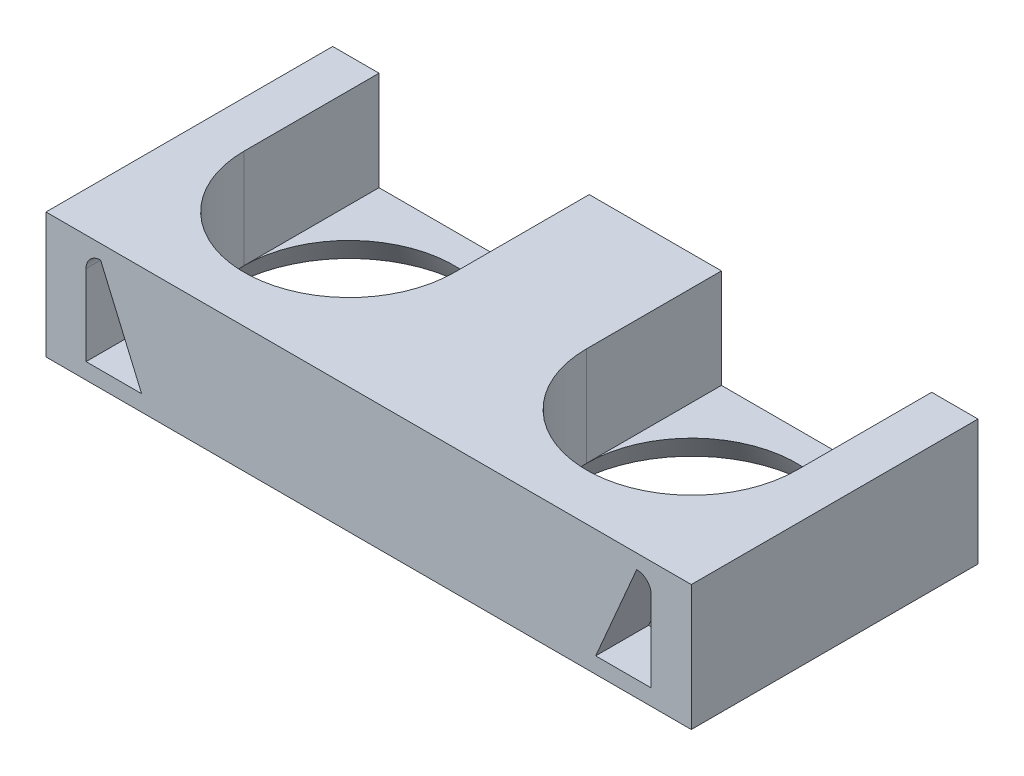
SolidWorks part; units mm, degrees
ref_plane "Alzado" through (0, 0, 0) normal (0, 0, 1) x (1, 0, 0)
ref_plane "Planta" through (0, 0, 0) normal (0, 1, 0) x (1, 0, 0)
ref_plane "Vista lateral" through (0, 0, 0) normal (1, 0, 0) x (0, 0, -1)
ref_plane "Plano1" through (0, -4.9, 0) normal (0, -1, 0) x (-1, 0, 0)
sketch "Croquis2" plane through (0, -4.9, 0) normal (0, -1, 0) x (-1, 0, 0)
  line L0 (-5, 20.4) -> (5, 20.4)
  line L1 (-12.95, 10.2) -> (12.95, 10.2) construction
  line L2 (-20.9, 10.2) -> (-20.9, 20.4)
  line L3 (20.9, 10.2) -> (20.9, 20.4)
  line L4 (-5, 10.2) -> (-5, 20.4)
  line L5 (5, 10.2) -> (5, 20.4)
  line L6 (-20.9, 20.4) -> (-24.404, 20.4)
  line L7 (-24.404, 20.4) -> (-24.404, -1.2848)
  line L8 (0, 10.2) -> (0, 20.4) construction
  line L9 (24.404, 20.4) -> (24.404, -1.2848)
  line L10 (-24.404, -1.2848) -> (24.404, -1.2848)
  line L11 (24.404, 20.4) -> (20.9, 20.4)
  circle A2 centre (-12.95, 10.2) radius 7.95
  arc A3 (-20.9, 10.2) -> (-5, 10.2) centre (-12.95, 10.2) ccw
  circle A5 centre (12.95, 10.2) radius 7.95
  arc A6 (5, 10.2) -> (20.9, 10.2) centre (12.95, 10.2) ccw
  dimension "D1" = 0
  dimension "D2" = 0
extrude "Saliente-Extruir1" add sketch "Croquis2" along normal blind 7.5
sketch "Croquis3" plane through (0, -12.4, 0) normal (0, -1, 0) x (1, 0, 0)
  line L11 (24.404, 1.2848) -> (-24.404, 1.2848)
  line L12 (24.404, 1.2848) -> (24.404, -20.4)
  line L13 (24.404, -20.4) -> (-24.404, -20.4)
  line L14 (-24.404, 1.2848) -> (-24.404, -20.4)
extrude "Saliente-Extruir2" add sketch "Croquis3" along normal blind 2
sketch "Croquis4" plane through (0, -12.4, 0) normal (0, -1, 0) x (1, 0, 0)
  circle A1 centre (-12.95, -10.2) radius 7.95
  circle A2 centre (12.95, -10.2) radius 7.95
extrude "Cortar-Extruir1" cut sketch "Croquis4" along normal blind 3 draft 30 draft outward yes
ref_plane "Plano2" through (0, 0, 0) normal (1, 0, 0) x (0, 0, -1)
sketch "Croquis7" plane through (0, 0, 1.2848) normal (0, 0, 1) x (1, 0, 0)
  line L0 (20.2732, -12.0884) -> (20.2732, -7.0884) construction
  line L1 (19.1732, -12.0884) -> (19.1732, -7.0884) construction
  line L2 (21.3732, -12.0884) -> (21.3732, -7.0884) construction
  line L3 (20.2732, -9.5884) -> (18.2732, -9.5884) construction
  line L4 (20.2732, -10.6884) -> (18.2732, -10.6884) construction
  line L5 (20.2732, -8.4884) -> (18.2732, -8.4884) construction
  line L6 (0, -14.4) -> (0, -4.9) construction
  line L7 (24.404, -14.4) -> (-24.404, -14.4) construction
  line L8 (24.404, -4.9) -> (-24.404, -4.9) construction
  line L9 (-20.2732, -9.5884) -> (-18.2732, -9.5884) construction
  line L10 (-20.2732, -10.6884) -> (-18.2732, -10.6884) construction
  line L11 (-20.2732, -8.4884) -> (-18.2732, -8.4884) construction
  line L12 (-20.2732, -12.0884) -> (-20.2732, -7.0884) construction
  line L13 (-19.1732, -12.0884) -> (-19.1732, -7.0884) construction
  line L14 (-21.3732, -12.0884) -> (-21.3732, -7.0884) construction
  line L15 (-21.3732, -7.0884) -> (-21.3732, -13.1884)
  line L16 (-21.3732, -5.9884) -> (-19.1732, -5.9884) construction
  line L17 (-21.3732, -7.0884) -> (-21.3732, -13.1884) construction
  line L18 (-21.3732, -13.1884) -> (-19.1732, -13.1884) construction
  line L19 (-19.1732, -5.9884) -> (-19.1732, -13.1884) construction
  line L20 (-21.3732, -5.9884) -> (-19.1732, -13.1884) construction
  line L21 (-21.3732, -13.1884) -> (-19.1732, -5.9884) construction
  line L22 (-19.1732, -13.1884) -> (-17.1732, -13.1884) construction
  line L23 (-19.1732, -13.1884) -> (-19.1732, -5.9884) construction
  line L24 (-19.1732, -5.9884) -> (-17.1732, -5.9884) construction
  line L25 (-17.1732, -13.1884) -> (-17.1732, -5.9884) construction
  line L26 (-21.3732, -13.1884) -> (-17.1732, -13.1884)
  line L27 (-17.1732, -13.1884) -> (-20.2732, -5.9884)
  line L28 (21.3732, -13.1884) -> (17.1732, -13.1884)
  line L29 (21.3732, -7.0884) -> (21.3732, -13.1884)
  line L30 (17.1732, -13.1884) -> (20.2732, -5.9884)
  arc A0 (19.1732, -12.0884) -> (21.3732, -12.0884) centre (20.2732, -12.0884) ccw construction
  arc A1 (21.3732, -7.0884) -> (19.1732, -7.0884) centre (20.2732, -7.0884) ccw construction
  arc A2 (20.2732, -10.6884) -> (20.2732, -8.4884) centre (20.2732, -9.5884) ccw construction
  arc A3 (18.2732, -8.4884) -> (18.2732, -10.6884) centre (18.2732, -9.5884) ccw construction
  arc A4 (-20.2732, -10.6884) -> (-20.2732, -8.4884) centre (-20.2732, -9.5884) cw construction
  arc A5 (-18.2732, -8.4884) -> (-18.2732, -10.6884) centre (-18.2732, -9.5884) cw construction
  arc A6 (-19.1732, -12.0884) -> (-21.3732, -12.0884) centre (-20.2732, -12.0884) cw construction
  arc A7 (-21.3732, -7.0884) -> (-20.2732, -5.9884) centre (-20.2732, -7.0884) cw construction
  arc A9 (20.2732, -5.9884) -> (21.3732, -7.0884) centre (20.2732, -7.0884) cw
  arc A11 (-20.2732, -5.9884) -> (-21.3732, -7.0884) centre (-20.2732, -7.0884) ccw
  point P4 (20.2732, -9.5884)
  point P9 (19.2732, -9.5884)
  point P25 (-19.2732, -9.5884)
  point P32 (-20.2732, -9.5884)
  point P41 (-20.2732, -9.5884)
extrude "Cortar-Extruir2" cut sketch "Croquis7" against normal blind 4 contours A5 L11 L13 L10 | A4 L10 L13 L11 | A7 L14 A4 L11 L13 | A6 L13 L10 A4 L14 | A2 L2 A1 L1 L5 | A2 L5 L1 L4 | A2 L4 L1 A0 L2 | L5 A3 L4 L1 | L27 A11 L15 L26 | A9 L30 L28 L29
